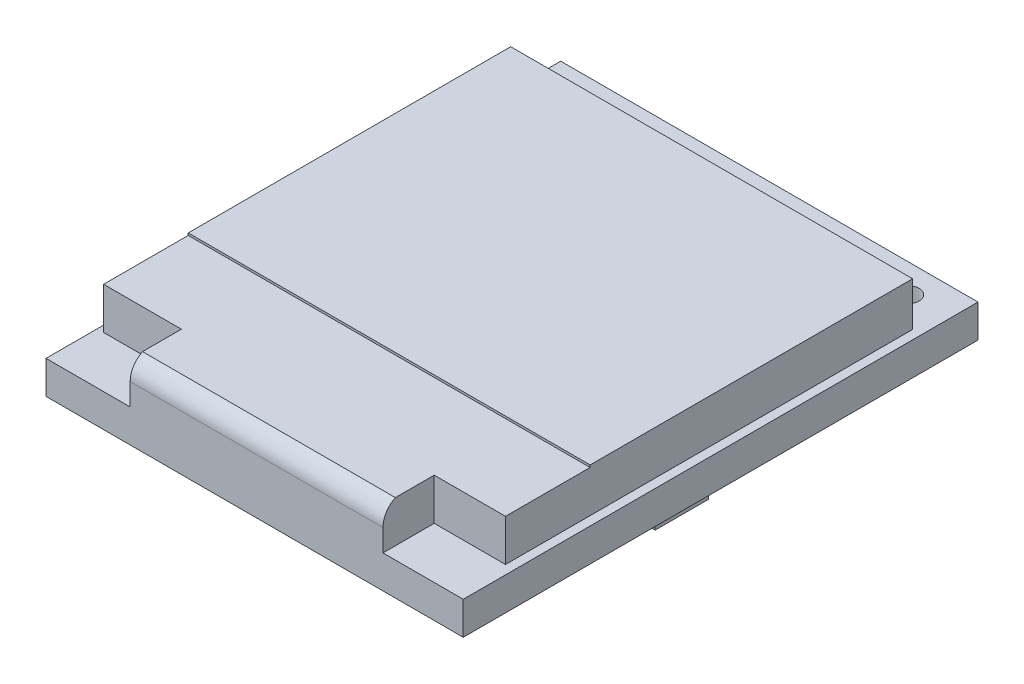
SolidWorks part; units mm, degrees
ref_plane "Front Plane" through (0, 0, 0) normal (0, 0, 1) x (1, 0, 0)
ref_plane "Top Plane" through (0, 0, 0) normal (0, 1, 0) x (1, 0, 0)
ref_plane "Right Plane" through (0, 0, 0) normal (1, 0, 0) x (0, 0, -1)
sketch "Sketch1" plane through (0, 0, 0) normal (0, 1, 0) x (1, 0, 0)
  line L0 (1.88, -1.3) -> (4.42, -1.3) construction
  line L1 (0, 0) -> (19, 0)
  line L2 (0, 0) -> (0, -23.44)
  line L3 (0, -23.44) -> (19, -23.44)
  line L4 (19, 0) -> (19, -23.44)
  circle A0 centre (1.88, -1.3) radius 0.5
  circle A1 centre (4.42, -1.3) radius 0.5
  circle A2 centre (6.96, -1.3) radius 0.5
  circle A3 centre (9.5, -1.3) radius 0.5
  circle A4 centre (12.04, -1.3) radius 0.5
  circle A5 centre (14.58, -1.3) radius 0.5
  circle A6 centre (17.12, -1.3) radius 0.5
  dimension "D3" = 7
  dimension "D5" = 1
  dimension "D1" = 19
  dimension "D2" = 23.44
  dimension "D4" = 2.54
  dimension "D6" = 1.88
  dimension "D7" = 1.3
extrude "Boss-Extrude1" add sketch "Sketch1" along normal blind 1.5
sketch "Sketch3" plane through (0, 1.5, 0) normal (0, 1, 0) x (1, 0, 0)
  line L0 (3.8324, -21.107) -> (3.8324, -23.44)
  line L1 (0.2901, -2.5692) -> (18.5918, -2.5692)
  line L2 (0.2901, -2.5692) -> (0.2901, -21.107)
  line L3 (0.2901, -21.107) -> (3.8324, -21.107)
  line L4 (18.5918, -2.5692) -> (18.5918, -21.107)
  line L5 (0, -23.44) -> (19, -23.44) construction
  line L6 (15.3447, -21.107) -> (15.3447, -23.44)
  line L7 (15.3447, -21.107) -> (18.5918, -21.107)
  line L8 (3.8324, -23.44) -> (15.3447, -23.44)
extrude "Boss-Extrude2" add sketch "Sketch3" along normal blind 2
fillet "Fillet1" radius 1 1 edges at (9.5886, 3.5, 23.44)
sketch "Sketch4" plane through (0, 0, 0) normal (0, -1, 0) x (1, 0, 0)
  line L1 (6.6198, 7.1483) -> (3.6958, 7.1483)
  line L2 (6.6198, 7.1483) -> (6.6198, 9.2637)
  line L3 (6.6198, 9.2637) -> (3.6958, 9.2637)
  line L4 (3.6958, 7.1483) -> (3.6958, 9.2637)
extrude "Boss-Extrude3" add sketch "Sketch4" along normal blind 1
sketch "Sketch5" plane through (0, 0, 0) normal (0, -1, 0) x (1, 0, 0)
  line L0 (2.9941, 11.6566) -> (2.9941, 14.0991)
  line L1 (1.4541, 11.6566) -> (0.4884, 11.6566)
  line L2 (1.4541, 11.6566) -> (1.4541, 14.0991)
  line L3 (1.4541, 14.0991) -> (0.4884, 14.0991)
  line L4 (0.4884, 11.6566) -> (0.4884, 14.0991)
  line L5 (2.9941, 11.6566) -> (2.0284, 11.6566)
  line L6 (2.0284, 11.6566) -> (2.0284, 14.0991)
  line L7 (2.9941, 14.0991) -> (2.0284, 14.0991)
  line L8 (4.5341, 11.6566) -> (4.5341, 14.0991)
  line L9 (4.5341, 11.6566) -> (3.5684, 11.6566)
  line L10 (3.5684, 11.6566) -> (3.5684, 14.0991)
  line L11 (4.5341, 14.0991) -> (3.5684, 14.0991)
  line L12 (6.0741, 11.6566) -> (6.0741, 14.0991)
  line L13 (6.0741, 11.6566) -> (5.1084, 11.6566)
  line L14 (5.1084, 11.6566) -> (5.1084, 14.0991)
  line L15 (6.0741, 14.0991) -> (5.1084, 14.0991)
  line L16 (7.6141, 11.6566) -> (7.6141, 14.0991)
  line L17 (7.6141, 11.6566) -> (6.6484, 11.6566)
  line L18 (6.6484, 11.6566) -> (6.6484, 14.0991)
  line L19 (7.6141, 14.0991) -> (6.6484, 14.0991)
  line L20 (9.1541, 11.6566) -> (9.1541, 14.0991) [skipped]
  line L21 (9.1541, 11.6566) -> (8.1884, 11.6566) [skipped]
  line L22 (8.1884, 11.6566) -> (8.1884, 14.0991) [skipped]
  line L23 (9.1541, 14.0991) -> (8.1884, 14.0991) [skipped]
  line L24 (10.6941, 11.6566) -> (10.6941, 14.0991)
  line L25 (10.6941, 11.6566) -> (9.7284, 11.6566)
  line L26 (9.7284, 11.6566) -> (9.7284, 14.0991)
  line L27 (10.6941, 14.0991) -> (9.7284, 14.0991)
  line L28 (12.2341, 11.6566) -> (12.2341, 14.0991)
  line L29 (12.2341, 11.6566) -> (11.2684, 11.6566)
  line L30 (11.2684, 11.6566) -> (11.2684, 14.0991)
  line L31 (12.2341, 14.0991) -> (11.2684, 14.0991)
  line L32 (13.7741, 11.6566) -> (13.7741, 14.0991) [skipped]
  line L33 (13.7741, 11.6566) -> (12.8084, 11.6566) [skipped]
  line L34 (12.8084, 11.6566) -> (12.8084, 14.0991) [skipped]
  line L35 (13.7741, 14.0991) -> (12.8084, 14.0991) [skipped]
  line L36 (15.3141, 11.6566) -> (15.3141, 14.0991)
  line L37 (15.3141, 11.6566) -> (14.3484, 11.6566)
  line L38 (14.3484, 11.6566) -> (14.3484, 14.0991)
  line L39 (15.3141, 14.0991) -> (14.3484, 14.0991)
  line L40 (16.8541, 11.6566) -> (16.8541, 14.0991)
  line L41 (16.8541, 11.6566) -> (15.8884, 11.6566)
  line L42 (15.8884, 11.6566) -> (15.8884, 14.0991)
  line L43 (16.8541, 14.0991) -> (15.8884, 14.0991)
  line L44 (18.3941, 11.6566) -> (18.3941, 14.0991)
  line L45 (18.3941, 11.6566) -> (17.4284, 11.6566)
  line L46 (17.4284, 11.6566) -> (17.4284, 14.0991)
  line L47 (18.3941, 14.0991) -> (17.4284, 14.0991)
  line L48 (2.9941, 7.0566) -> (2.0284, 7.0566)
  line L49 (2.9941, 7.0566) -> (2.9941, 9.4991)
  line L50 (2.9941, 9.4991) -> (2.0284, 9.4991)
  line L51 (2.0284, 7.0566) -> (2.0284, 9.4991)
  dimension "D1" = 12
  dimension "D2" = 2
extrude "Boss-Extrude4" add sketch "Sketch5" along normal blind 0.75
sketch "Sketch6" plane through (0, 3.5, 0) normal (0, 1, 0) x (1, 0, 0)
  line L0 (0.2901, -17.2538) -> (18.5918, -17.2538)
  line L1 (0.2901, -2.5692) -> (0.2901, -21.107) construction
  line L2 (18.5918, -21.107) -> (18.5918, -2.5692) construction
  line L3 (18.5918, -17.2538) -> (18.5918, -21.107)
  line L4 (18.5918, -21.107) -> (15.3447, -21.107)
  line L5 (0.2901, -21.107) -> (3.8324, -21.107) construction
  line L6 (3.8324, -21.107) -> (3.8324, -23.44) construction
  line L7 (15.3447, -23.44) -> (3.8324, -23.44) construction
  line L8 (15.3447, -23.44) -> (15.3447, -21.107) construction
  line L9 (0.2901, -21.107) -> (3.8324, -21.107)
  line L10 (3.8324, -21.107) -> (3.8324, -23.44)
  line L11 (15.3447, -23.44) -> (3.8324, -23.44)
  line L12 (15.3447, -23.44) -> (15.3447, -21.107)
  line L13 (0.2901, -17.2538) -> (0.2901, -21.107)
  dimension "D1" = 6.1862
extrude "Cut-Extrude1" cut sketch "Sketch6" against normal blind 0.1
